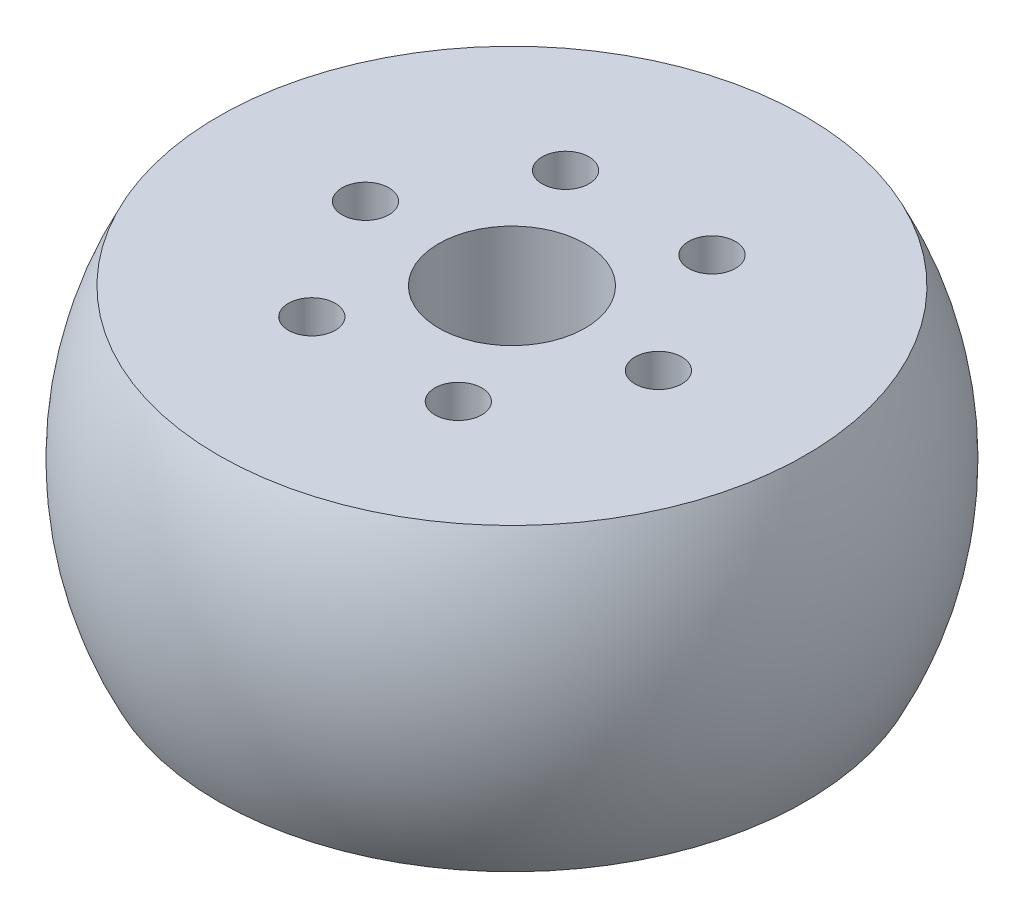
SolidWorks part; units mm, degrees
ref_plane "Front Plane" through (0, 0, 0) normal (0, 0, 1) x (1, 0, 0)
ref_plane "Top Plane" through (0, 0, 0) normal (0, 1, 0) x (1, 0, 0)
ref_plane "Right Plane" through (0, 0, 0) normal (1, 0, 0) x (0, 0, -1)
sketch "Sketch1" plane through (0, 0, 0) normal (1, 0, 0) x (0, 0, -1)
  line L0 (0, -6.5) -> (0, 6.5) construction
  line L1 (3.175, 6.5) -> (12.7233, 6.5)
  line L2 (3.175, 6.5) -> (3.175, -6.5)
  line L3 (3.175, -6.5) -> (12.7233, -6.5)
  line L4 (14.2875, 0) -> (0, 0) construction
  circle A0 centre (0, 0) radius 14.2875 construction
  arc A1 (12.7233, 6.5) -> (12.7233, -6.5) centre (0, 0) cw
  point P4 (0, 0)
  dimension "D1" = 6.35
  dimension "D2" = 13
  dimension "D3" = 14.2875
revolve "Revolve1" add sketch "Sketch1" angle 360 about L0
sketch "Sketch3" plane through (0, 0, 0) normal (0, 1, 0) x (1, 0, 0)
  line L0 (0, 0) -> (6.35, 0) construction
  circle A0 centre (6.35, 0) radius 1.016
  dimension "D1" = 2.032
  dimension "D2" = 6.35
extrude "Cut-Extrude1" cut sketch "Sketch3" against normal through all both and the other way through all
pattern_circular "CirPattern1" count 6 over 360 about axis through (0, 0, 0) along (0, 1, 0) of "Cut-Extrude1"
sketch "Sketch4" plane through (0, 0, 0) normal (0, 1, 0) x (1, 0, 0)
  point P0 (0, 0)
